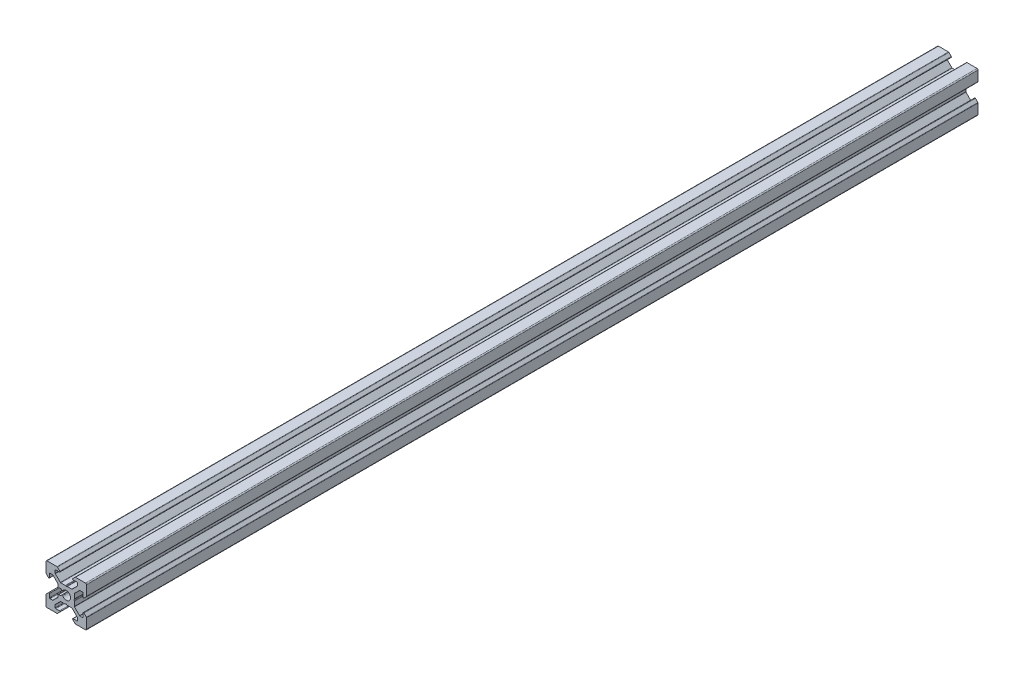
SolidWorks part; units mm, degrees
material "1060 Alloy"
ref_plane "Front Plane" through (0, 0, 0) normal (0, 0, 1) x (1, 0, 0)
ref_plane "Top Plane" through (0, 0, 0) normal (0, 1, 0) x (1, 0, 0)
ref_plane "Right Plane" through (0, 0, 0) normal (1, 0, 0) x (0, 0, -1)
sketch "Model" plane through (0, 0, 0) normal (0, 0, 1) x (1, 0, 0)
  line L266 (2013.2312, 1378.5004) -> (2014.1312, 1378.5004)
  line L267 (2014.3433, 1378.5883) -> (2014.6884, 1378.9333)
  line L268 (2014.6884, 1381.0674) -> (2014.3433, 1381.4125)
  line L269 (2014.1312, 1381.5004) -> (2013.2312, 1381.5004)
  line L270 (2012.9312, 1381.8004) -> (2012.9312, 1382.7004)
  line L271 (2012.8433, 1382.9125) -> (2010.3787, 1385.3772)
  line L272 (2010.2019, 1385.4504) -> (2008.8812, 1385.4504)
  line L273 (2008.6312, 1385.2004) -> (2008.6312, 1383.3504)
  line L274 (2008.2044, 1383.1736) -> (2007.0191, 1384.359)
  line L275 (2006.9312, 1384.5711) -> (2006.9312, 1389.5004)
  line L276 (2007.4312, 1390.0004) -> (2012.3605, 1390.0004)
  line L277 (2012.5726, 1389.9125) -> (2013.758, 1388.7272)
  line L278 (2013.5812, 1388.3004) -> (2011.7312, 1388.3004)
  line L279 (2011.4812, 1388.0504) -> (2011.4812, 1386.7297)
  line L280 (2011.5544, 1386.5529) -> (2014.0338, 1384.0736)
  line L281 (2014.2105, 1384.0004) -> (2016.4702, 1384.0004)
  line L282 (2017.3922, 1384.0004) -> (2019.6519, 1384.0004)
  line L283 (2019.8287, 1384.0736) -> (2022.308, 1386.5529)
  line L284 (2022.3812, 1386.7297) -> (2022.3812, 1388.0504)
  line L285 (2022.1312, 1388.3004) -> (2020.2812, 1388.3004)
  line L286 (2020.1044, 1388.7272) -> (2021.2898, 1389.9125)
  line L287 (2021.5019, 1390.0004) -> (2026.4312, 1390.0004)
  line L288 (2026.9312, 1389.5004) -> (2026.9312, 1384.5711)
  line L289 (2026.8433, 1384.359) -> (2025.658, 1383.1736)
  line L290 (2025.2312, 1383.3504) -> (2025.2312, 1385.2004)
  line L291 (2024.9812, 1385.4504) -> (2023.6605, 1385.4504)
  line L292 (2023.4838, 1385.3772) -> (2021.0044, 1382.8978)
  line L293 (2020.9312, 1382.7211) -> (2020.9312, 1380.4614)
  line L294 (2020.9312, 1379.5394) -> (2020.9312, 1377.2797)
  line L295 (2021.0044, 1377.1029) -> (2023.4838, 1374.6236)
  line L296 (2023.6605, 1374.5504) -> (2024.9812, 1374.5504)
  line L297 (2025.2312, 1374.8004) -> (2025.2312, 1376.6504)
  line L298 (2025.658, 1376.8272) -> (2026.8433, 1375.6418)
  line L299 (2026.9312, 1375.4297) -> (2026.9312, 1370.5004)
  line L300 (2026.4312, 1370.0004) -> (2021.5019, 1370.0004)
  line L301 (2021.2898, 1370.0883) -> (2020.1044, 1371.2736)
  line L302 (2020.2812, 1371.7004) -> (2022.1312, 1371.7004)
  line L303 (2022.3812, 1371.9504) -> (2022.3812, 1373.2711)
  line L304 (2022.308, 1373.4478) -> (2019.8287, 1375.9272)
  line L305 (2019.6519, 1376.0004) -> (2017.3922, 1376.0004)
  line L306 (2016.4702, 1376.0004) -> (2014.2105, 1376.0004)
  line L307 (2014.0338, 1375.9272) -> (2011.5544, 1373.4478)
  line L308 (2011.4812, 1373.2711) -> (2011.4812, 1371.9504)
  line L309 (2011.7312, 1371.7004) -> (2013.5812, 1371.7004)
  line L310 (2013.758, 1371.2736) -> (2012.5726, 1370.0883)
  line L311 (2012.3605, 1370.0004) -> (2007.4312, 1370.0004)
  line L312 (2006.9312, 1370.5004) -> (2006.9312, 1375.4297)
  line L313 (2007.0191, 1375.6418) -> (2008.2044, 1376.8272)
  line L314 (2008.6312, 1376.6504) -> (2008.6312, 1374.8004)
  line L315 (2008.8812, 1374.5504) -> (2010.2019, 1374.5504)
  line L316 (2010.3787, 1374.6236) -> (2012.8433, 1377.0883)
  line L317 (2012.9312, 1377.3004) -> (2012.9312, 1378.2004)
  arc A420 (2013.2312, 1378.5004) -> (2012.9312, 1378.2004) centre (2013.2312, 1378.2004) ccw
  arc A421 (2014.1312, 1378.5004) -> (2014.3433, 1378.5883) centre (2014.1312, 1378.8004) ccw
  arc A422 (2015.1544, 1378.8811) -> (2014.6884, 1378.9333) centre (2014.9005, 1378.7212) ccw
  arc A423 (2015.1544, 1378.8811) -> (2015.1544, 1381.1197) centre (2016.9312, 1380.0004) ccw
  arc A424 (2014.6884, 1381.0674) -> (2015.1544, 1381.1197) centre (2014.9005, 1381.2796) ccw
  arc A425 (2014.3433, 1381.4125) -> (2014.1312, 1381.5004) centre (2014.1312, 1381.2004) ccw
  arc A426 (2012.9312, 1381.8004) -> (2013.2312, 1381.5004) centre (2013.2312, 1381.8004) ccw
  arc A427 (2012.9312, 1382.7004) -> (2012.8433, 1382.9125) centre (2012.6312, 1382.7004) ccw
  arc A428 (2010.3787, 1385.3772) -> (2010.2019, 1385.4504) centre (2010.2019, 1385.2004) ccw
  arc A429 (2008.8812, 1385.4504) -> (2008.6312, 1385.2004) centre (2008.8812, 1385.2004) ccw
  arc A430 (2008.2044, 1383.1736) -> (2008.6312, 1383.3504) centre (2008.3812, 1383.3504) ccw
  arc A431 (2006.9312, 1384.5711) -> (2007.0191, 1384.359) centre (2007.2312, 1384.5711) ccw
  arc A432 (2007.4312, 1390.0004) -> (2006.9312, 1389.5004) centre (2007.4312, 1389.5004) ccw
  arc A433 (2012.5726, 1389.9125) -> (2012.3605, 1390.0004) centre (2012.3605, 1389.7004) ccw
  arc A434 (2013.5812, 1388.3004) -> (2013.758, 1388.7272) centre (2013.5812, 1388.5504) ccw
  arc A435 (2011.7312, 1388.3004) -> (2011.4812, 1388.0504) centre (2011.7312, 1388.0504) ccw
  arc A436 (2011.4812, 1386.7297) -> (2011.5544, 1386.5529) centre (2011.7312, 1386.7297) ccw
  arc A437 (2014.0338, 1384.0736) -> (2014.2105, 1384.0004) centre (2014.2105, 1384.2504) ccw
  arc A438 (2016.7217, 1383.864) -> (2016.4702, 1384.0004) centre (2016.4702, 1383.7004) ccw
  arc A439 (2016.7217, 1383.864) -> (2017.1407, 1383.864) centre (2016.9312, 1384.0004) ccw
  arc A440 (2017.3922, 1384.0004) -> (2017.1407, 1383.864) centre (2017.3922, 1383.7004) ccw
  arc A441 (2019.6519, 1384.0004) -> (2019.8287, 1384.0736) centre (2019.6519, 1384.2504) ccw
  arc A442 (2022.308, 1386.5529) -> (2022.3812, 1386.7297) centre (2022.1312, 1386.7297) ccw
  arc A443 (2022.3812, 1388.0504) -> (2022.1312, 1388.3004) centre (2022.1312, 1388.0504) ccw
  arc A444 (2020.1044, 1388.7272) -> (2020.2812, 1388.3004) centre (2020.2812, 1388.5504) ccw
  arc A445 (2021.5019, 1390.0004) -> (2021.2898, 1389.9125) centre (2021.5019, 1389.7004) ccw
  arc A446 (2026.9312, 1389.5004) -> (2026.4312, 1390.0004) centre (2026.4312, 1389.5004) ccw
  arc A447 (2026.8433, 1384.359) -> (2026.9312, 1384.5711) centre (2026.6312, 1384.5711) ccw
  arc A448 (2025.2312, 1383.3504) -> (2025.658, 1383.1736) centre (2025.4812, 1383.3504) ccw
  arc A449 (2025.2312, 1385.2004) -> (2024.9812, 1385.4504) centre (2024.9812, 1385.2004) ccw
  arc A450 (2023.6605, 1385.4504) -> (2023.4838, 1385.3772) centre (2023.6605, 1385.2004) ccw
  arc A451 (2021.0044, 1382.8978) -> (2020.9312, 1382.7211) centre (2021.1812, 1382.7211) ccw
  arc A452 (2020.7948, 1380.2099) -> (2020.9312, 1380.4614) centre (2020.6312, 1380.4614) ccw
  arc A453 (2020.7948, 1380.2099) -> (2020.7948, 1379.7909) centre (2020.9312, 1380.0004) ccw
  arc A454 (2020.9312, 1379.5394) -> (2020.7948, 1379.7909) centre (2020.6312, 1379.5394) ccw
  arc A455 (2020.9312, 1377.2797) -> (2021.0044, 1377.1029) centre (2021.1812, 1377.2797) ccw
  arc A456 (2023.4838, 1374.6236) -> (2023.6605, 1374.5504) centre (2023.6605, 1374.8004) ccw
  arc A457 (2024.9812, 1374.5504) -> (2025.2312, 1374.8004) centre (2024.9812, 1374.8004) ccw
  arc A458 (2025.658, 1376.8272) -> (2025.2312, 1376.6504) centre (2025.4812, 1376.6504) ccw
  arc A459 (2026.9312, 1375.4297) -> (2026.8433, 1375.6418) centre (2026.6312, 1375.4297) ccw
  arc A460 (2026.4312, 1370.0004) -> (2026.9312, 1370.5004) centre (2026.4312, 1370.5004) ccw
  arc A461 (2021.2898, 1370.0883) -> (2021.5019, 1370.0004) centre (2021.5019, 1370.3004) ccw
  arc A462 (2020.2812, 1371.7004) -> (2020.1044, 1371.2736) centre (2020.2812, 1371.4504) ccw
  arc A463 (2022.1312, 1371.7004) -> (2022.3812, 1371.9504) centre (2022.1312, 1371.9504) ccw
  arc A464 (2022.3812, 1373.2711) -> (2022.308, 1373.4478) centre (2022.1312, 1373.2711) ccw
  arc A465 (2019.8287, 1375.9272) -> (2019.6519, 1376.0004) centre (2019.6519, 1375.7504) ccw
  arc A466 (2017.1407, 1376.1368) -> (2017.3922, 1376.0004) centre (2017.3922, 1376.3004) ccw
  arc A467 (2017.1407, 1376.1368) -> (2016.7217, 1376.1368) centre (2016.9312, 1376.0004) ccw
  arc A468 (2016.4702, 1376.0004) -> (2016.7217, 1376.1368) centre (2016.4702, 1376.3004) ccw
  arc A469 (2014.2105, 1376.0004) -> (2014.0338, 1375.9272) centre (2014.2105, 1375.7504) ccw
  arc A470 (2011.5544, 1373.4478) -> (2011.4812, 1373.2711) centre (2011.7312, 1373.2711) ccw
  arc A471 (2011.4812, 1371.9504) -> (2011.7312, 1371.7004) centre (2011.7312, 1371.9504) ccw
  arc A472 (2013.758, 1371.2736) -> (2013.5812, 1371.7004) centre (2013.5812, 1371.4504) ccw
  arc A473 (2012.3605, 1370.0004) -> (2012.5726, 1370.0883) centre (2012.3605, 1370.3004) ccw
  arc A474 (2006.9312, 1370.5004) -> (2007.4312, 1370.0004) centre (2007.4312, 1370.5004) ccw
  arc A475 (2007.0191, 1375.6418) -> (2006.9312, 1375.4297) centre (2007.2312, 1375.4297) ccw
  arc A476 (2008.6312, 1376.6504) -> (2008.2044, 1376.8272) centre (2008.3812, 1376.6504) ccw
  arc A477 (2008.6312, 1374.8004) -> (2008.8812, 1374.5504) centre (2008.8812, 1374.8004) ccw
  arc A478 (2010.2019, 1374.5504) -> (2010.3787, 1374.6236) centre (2010.2019, 1374.8004) ccw
  arc A479 (2012.8433, 1377.0883) -> (2012.9312, 1377.3004) centre (2012.6312, 1377.3004) ccw
extrude "Boss-Extrude1" add sketch "Model" along normal blind 440
